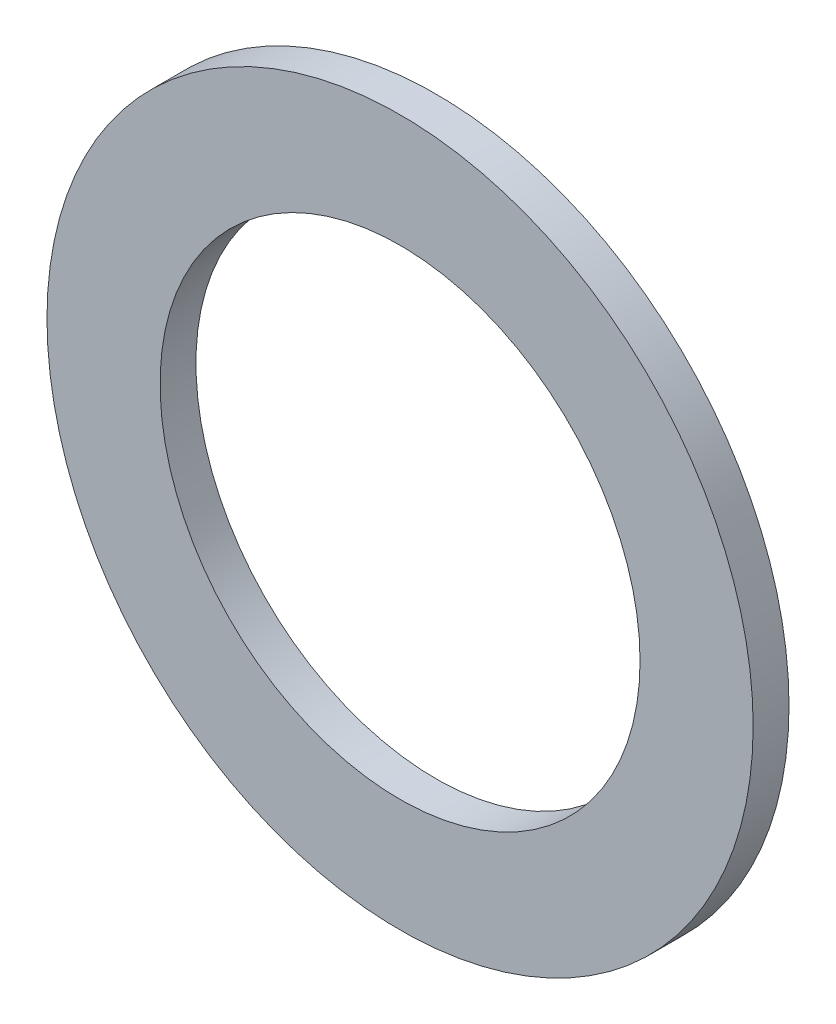
SolidWorks part; units mm, degrees
material "Bismuth"
ref_plane "Front" through (0, 0, 0) normal (0, 0, 1) x (1, 0, 0)
ref_plane "Top" through (0, 0, 0) normal (0, 1, 0) x (1, 0, 0)
ref_plane "Right" through (0, 0, 0) normal (1, 0, 0) x (0, 0, -1)
sketch "Sketch1" plane through (0, 0, 0) normal (0, 0, 1) x (1, 0, 0)
  circle A0 centre (0, 0) radius 128
  circle A1 centre (0, 0) radius 87
extrude "Boss-Extrude1" add sketch "Sketch1" along normal blind 13
